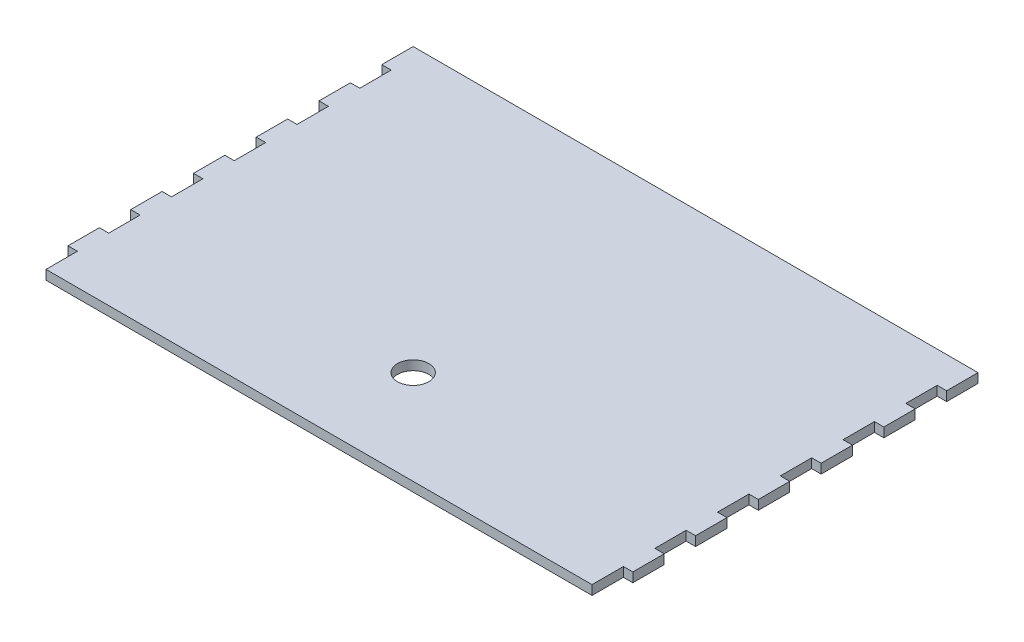
SolidWorks part; units mm, degrees
ref_plane "Plan de face" through (0, 0, 0) normal (0, 0, 1) x (1, 0, 0)
ref_plane "Plan de dessus" through (0, 0, 0) normal (0, 1, 0) x (1, 0, 0)
ref_plane "Plan de droite" through (0, 0, 0) normal (1, 0, 0) x (0, 0, -1)
sketch "Esquisse1" plane through (0, 0, 0) normal (0, 1, 0) x (1, 0, 0)
  line L0 (-90, 60) -> (90, -60) construction
  line L1 (-90, 60) -> (90, 60)
  line L2 (-90, 60) -> (-90, 50)
  line L3 (-87, -60) -> (87, -60)
  line L4 (90, 60) -> (90, 50)
  line L5 (0, -55) -> (0, 55) construction
  line L6 (-90, 50) -> (-87, 50)
  line L8 (-90, 40) -> (-87, 40)
  line L9 (-87, 50) -> (-87, 40)
  line L10 (90, 40) -> (87, 40)
  line L11 (87, 50) -> (87, 40)
  line L12 (90, 50) -> (87, 50)
  line L15 (-90, 30) -> (-87, 30)
  line L16 (-87, 30) -> (-87, 20)
  line L17 (-90, 20) -> (-87, 20)
  line L18 (90, 20) -> (87, 20)
  line L19 (87, 30) -> (87, 20)
  line L20 (90, 30) -> (87, 30)
  line L23 (-90, 10) -> (-87, 10)
  line L24 (-87, 10) -> (-87, 0)
  line L25 (-90, 0) -> (-87, 0)
  line L26 (90, 0) -> (87, 0)
  line L27 (87, 10) -> (87, 0)
  line L28 (90, 10) -> (87, 10)
  line L31 (-90, -10) -> (-87, -10)
  line L32 (-87, -10) -> (-87, -20)
  line L33 (-90, -20) -> (-87, -20)
  line L34 (90, -20) -> (87, -20)
  line L35 (87, -10) -> (87, -20)
  line L36 (90, -10) -> (87, -10)
  line L39 (-90, -30) -> (-87, -30)
  line L40 (-87, -30) -> (-87, -40)
  line L41 (-90, -40) -> (-87, -40)
  line L42 (90, -40) -> (87, -40)
  line L43 (87, -30) -> (87, -40)
  line L44 (90, -30) -> (87, -30)
  line L47 (-90, -50) -> (-87, -50)
  line L48 (-87, -50) -> (-87, -60)
  line L51 (87, -50) -> (87, -60)
  line L52 (90, -50) -> (87, -50)
  line L54 (-90, 40) -> (-90, 30)
  line L55 (-90, 20) -> (-90, 10)
  line L56 (-90, 0) -> (-90, -10)
  line L57 (-90, -20) -> (-90, -30)
  line L58 (-90, -40) -> (-90, -50)
  line L59 (-90, -60) -> (-87, -60) [skipped]
  line L60 (90, 40) -> (90, 30)
  line L61 (90, 20) -> (90, 10)
  line L62 (90, 0) -> (90, -10)
  line L63 (90, -20) -> (90, -30)
  line L64 (90, -40) -> (90, -50)
  line L65 (90, -60) -> (87, -60) [skipped]
  circle A0 centre (0, -30) radius 5
  point P4 (0, 0)
  dimension "D2" = 10
  dimension "D1" = 180
  dimension "D3" = 10
  dimension "D4" = 3
  dimension "D5" = 10
  dimension "D7" = 90
  dimension "D6" = 6
extrude "Boss.-Extru.1" add sketch "Esquisse1" along normal blind 3
